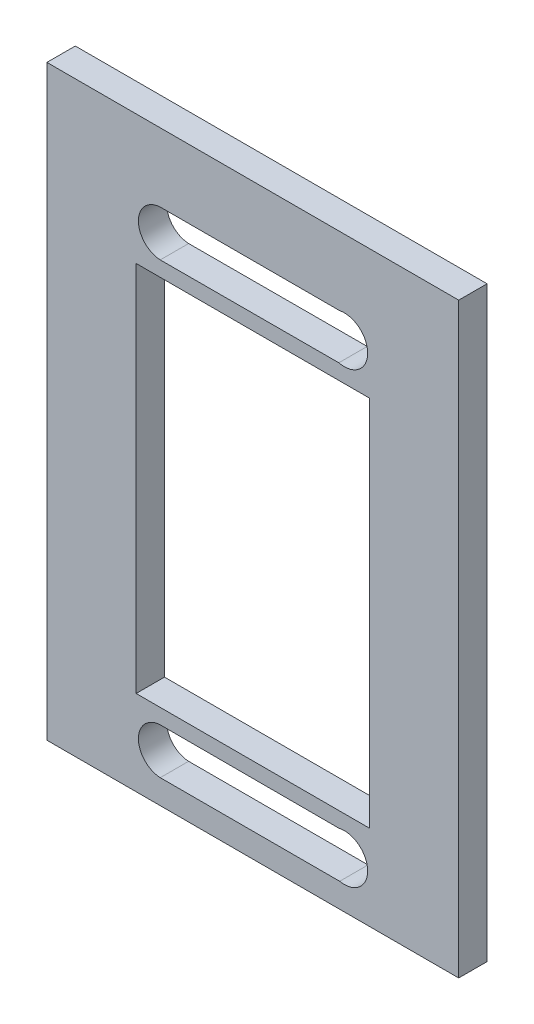
SolidWorks part; units mm, degrees
material "Teak"
ref_plane "Front Plane" through (0, 0, 0) normal (0, 0, 1) x (1, 0, 0)
ref_plane "Top Plane" through (0, 0, 0) normal (0, 1, 0) x (1, 0, 0)
ref_plane "Right Plane" through (0, 0, 0) normal (1, 0, 0) x (0, 0, -1)
sketch "Sketch1" plane through (0, 0, 0) normal (0, 0, 1) x (1, 0, 0)
  line L0 (0, 40) -> (0, 0) construction
  line L1 (0, -10.35) -> (54.3577, -10.35) construction
  line L2 (-12.75, -30.7) -> (12.75, -30.7)
  line L3 (-12.75, -30.7) -> (-12.75, 10)
  line L4 (-12.75, 10) -> (12.75, 10)
  line L5 (12.75, -30.7) -> (12.75, 10)
  line L6 (-12.75, -30.7) -> (12.75, 10) construction
  line L7 (-10.115, 16.65) -> (9.4933, 16.65)
  line L8 (0, 0) -> (55.631, 0) construction
  line L9 (-10.115, 11.65) -> (9.3986, 11.6711)
  line L10 (10, 14.15) -> (-10, 14.15) construction
  line L11 (10, -34.85) -> (-10, -34.85) construction
  line L12 (0, -60.7) -> (0, -20.7) construction
  line L13 (-10.115, -32.35) -> (9.3986, -32.3711)
  line L14 (-12.75, 10) -> (12.75, -30.7) construction
  line L15 (-22.5, -40) -> (22.5, -40)
  line L16 (-22.5, -40) -> (-22.5, 40)
  line L17 (-22.5, 40) -> (22.5, 40)
  line L18 (22.5, -40) -> (22.5, 40)
  line L19 (-10.115, -37.35) -> (9.4933, -37.35)
  circle A0 centre (0, 0) radius 3.4354 construction
  arc A1 (9.4933, 16.65) -> (9.3986, 11.6711) centre (10, 14.15) cw
  arc A2 (-10.115, 16.65) -> (-10.115, 11.65) centre (-10, 14.15) ccw
  arc A3 (-10.115, -37.35) -> (-10.115, -32.35) centre (-10, -34.85) cw
  arc A4 (9.4933, -37.35) -> (9.3986, -32.3711) centre (10, -34.85) ccw
  point P0 (0, 0)
  point P1 (0, -10.35)
  point P12 (0, 27)
  point P18 (0, 24.5)
  point P20 (0, 22)
  point P29 (0, -42.7)
  point P35 (0, -45.2)
  point P36 (0, -47.7)
  point P37 (0, 14.15)
  dimension "D4" = 49
  dimension "D1" = 10
  dimension "D2" = 40.7
  dimension "D3" = 25.5
  dimension "D5" = 20
  dimension "D6" = 0
  dimension "D7" = 45
  dimension "D8" = 80
extrude "Boss-Extrude1" add sketch "Sketch1" along normal blind 3.1
sketch "Sketch6" plane through (0, 0, 3.1) normal (0, 0, 1) x (1, 0, 0)
  line L1 (-22.5, 40) -> (22.5, 40)
  line L2 (-22.5, 40) -> (-22.5, -40)
  line L3 (-22.5, -40) -> (22.5, -40)
  line L4 (22.5, 40) -> (22.5, -40)
extrude "Boss-Extrude3" [suppressed] add sketch "Sketch6" against normal blind 3.1
sketch "Sketch7" plane through (0, 0, 0) normal (0, 0, 1) x (1, 0, 0)
  line L0 (-40, 40) -> (40, -40) construction
  line L1 (40, 40) -> (-40, -40) construction
  line L2 (-13.4704, 13.4704) -> (-13.4704, -13.4704) construction
  line L3 (-13.4704, 13.4704) -> (-11.4704, 13.4704) construction
  line L4 (0, 0) -> (57.4877, 0) construction
  line L5 (-11.4704, -13.4704) -> (-13.4704, -13.4704) construction
  line L6 (-15.4704, 13.4704) -> (-15.4704, -13.4704)
  line L7 (0, -40) -> (0, 40) construction
  line L8 (-15.4704, 13.4704) -> (-15.4704, 18.4704)
  line L9 (-15.4704, -13.4704) -> (-15.4704, -18.4704)
  line L10 (-11.4704, -13.4704) -> (-11.4704, -18.4704)
  line L11 (-11.4704, 13.4704) -> (-11.4704, -13.4704)
  line L12 (-11.4704, 13.4704) -> (-11.4704, 18.4704)
  line L13 (11.4704, -13.4704) -> (13.4704, -13.4704) construction
  line L14 (13.4704, 13.4704) -> (11.4704, 13.4704) construction
  line L15 (-40, -40) -> (40, -40)
  line L16 (-40, -40) -> (-40, 40)
  line L17 (-40, 40) -> (40, 40)
  line L18 (40, -40) -> (40, 40)
  line L19 (13.4704, 13.4704) -> (13.4704, -13.4704) construction
  line L20 (11.4704, 13.4704) -> (11.4704, 18.4704)
  line L21 (11.4704, 13.4704) -> (11.4704, -13.4704)
  line L22 (11.4704, -13.4704) -> (11.4704, -18.4704)
  line L23 (15.4704, -13.4704) -> (15.4704, -18.4704)
  line L24 (15.4704, 13.4704) -> (15.4704, 18.4704)
  line L25 (15.4704, 13.4704) -> (15.4704, -13.4704)
  arc A0 (-11.4704, 18.4704) -> (-15.4704, 18.4704) centre (-13.4704, 18.4704) ccw
  arc A1 (-15.4704, -18.4704) -> (-11.4704, -18.4704) centre (-13.4704, -18.4704) ccw
  arc A2 (15.4704, -18.4704) -> (11.4704, -18.4704) centre (13.4704, -18.4704) cw
  arc A3 (11.4704, 18.4704) -> (15.4704, 18.4704) centre (13.4704, 18.4704) cw
  circle A4 centre (0, 0) radius 9.525
  point P11 (0, 0)
  dimension "D1" = 26.9408
  dimension "D5" = 19.05
  dimension "D2" = 5
  dimension "D6" = 2
  dimension "D3" = 0
  dimension "D7" = 80
  dimension "D8" = 80
extrude "Cut-Extrude3" [suppressed] cut sketch "Sketch7" along normal through all flip side to cut
sketch "Sketch8" plane through (0, 0, 3.1) normal (0, 0, 1) x (1, 0, 0)
  line L1 (-22.5, 40) -> (22.5, 40)
  line L2 (-22.5, 40) -> (-22.5, 24.15)
  line L3 (-22.5, 24.15) -> (22.5, 24.15)
  line L4 (22.5, 40) -> (22.5, 24.15)
  line L5 (22.5, -40) -> (22.5, 40) construction
  line L6 (9.4933, 16.65) -> (-10.115, 16.65) construction
  dimension "D1" = 7.5
extrude "Cut-Extrude4" cut sketch "Sketch8" against normal through all
sketch "Sketch10" plane through (0, 0, 3.1) normal (0, 0, 1) x (1, 0, 0)
  line L0 (22.5, 24.15) -> (25.6, 24.15)
  line L1 (22.5, 24.15) -> (22.5, -45)
  line L2 (25.6, 24.15) -> (25.6, -45)
  line L3 (22.5, -45) -> (25.6, -45)
  line L4 (-22.5, -40) -> (22.5, -40) construction
  line L5 (14.4, -40) -> (19.4, -40)
  line L6 (14.4, -40) -> (14.4, -45)
  line L7 (19.4, -40) -> (19.4, -45)
  line L8 (14.4, -45) -> (19.4, -45)
  dimension "D1" = 3.1
  dimension "D2" = 5
  dimension "D3" = 3.1
  dimension "D4" = 5
  dimension "D5" = 0
equation "\"thick\" = 3.1mm"
equation "\"small_bearing_outer\"=12.9mm"
equation "\"servo1_L\"=40.7mm"
equation "\"servo1_W\"=20.5mm"
equation "\"servo1_H\"=43.5mm"
equation "\"servo1_hL\"=49mm"
equation "\"servo1_hW\"=10mm"
equation "\"D1@Boss-Extrude1\"=\"thick\""
equation "\"D2@Sketch1\"=\"servo1_L\""
equation "\"D4@Sketch1\"=\"servo1_hL\""
equation "\"D3@Sketch1\"=\"servo1_W\"+5mm"
equation "\"D1@Sketch10\"=\"thick\""
equation "\"D2@Sketch10\"=5mm"
equation "\"D3@Sketch10\"=\"thick\""
equation "\"D5@Sketch10\"=0"
